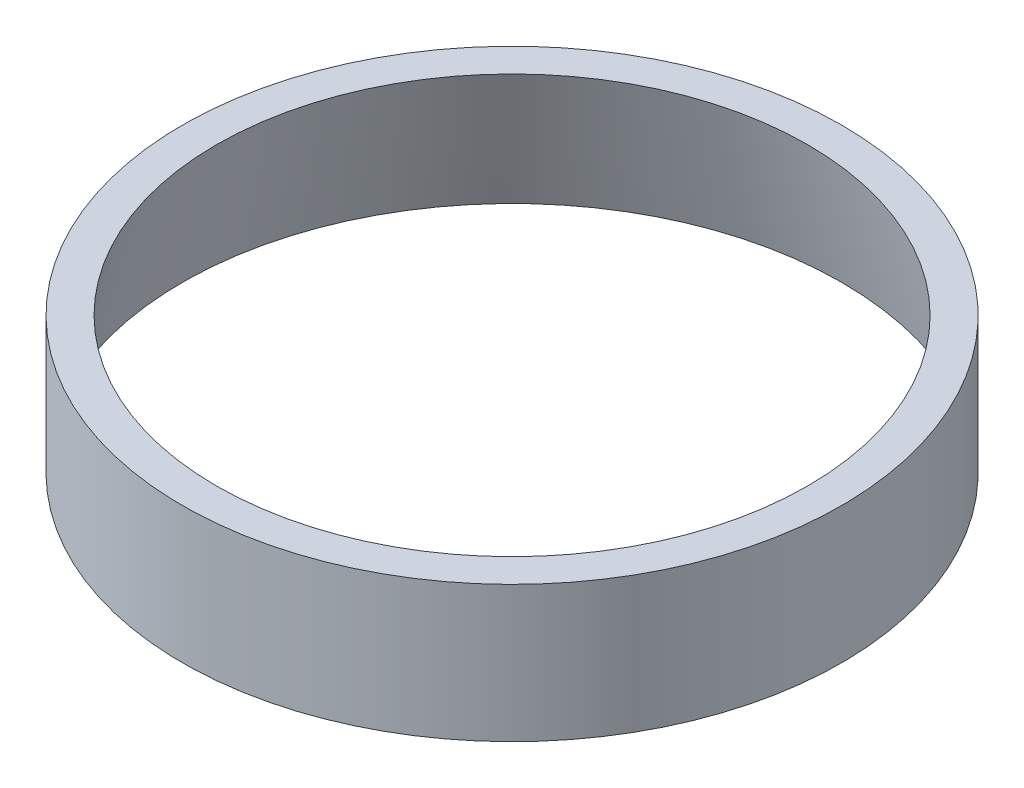
SolidWorks part; units mm, degrees
ref_plane "Front Plane" through (0, 0, 0) normal (0, 0, 1) x (1, 0, 0)
ref_plane "Top Plane" through (0, 0, 0) normal (0, 1, 0) x (1, 0, 0)
ref_plane "Right Plane" through (0, 0, 0) normal (1, 0, 0) x (0, 0, -1)
sketch "Sketch1" plane through (0, 0, 0) normal (0, 0, 1) x (1, 0, 0)
  line L0 (0, 0) -> (0, 823.5514) construction
  line L1 (37.5, 0) -> (33.6354, 15.5)
  line L2 (33.6354, 15.5) -> (37.5, 15.5)
  line L3 (37.5, 15.5) -> (37.5, 0)
  dimension "D1" = 37.5
  dimension "D2" = 104
  dimension "D3" = 15.5
revolve "Revolve1" add sketch "Sketch1" angle 360 about L0
